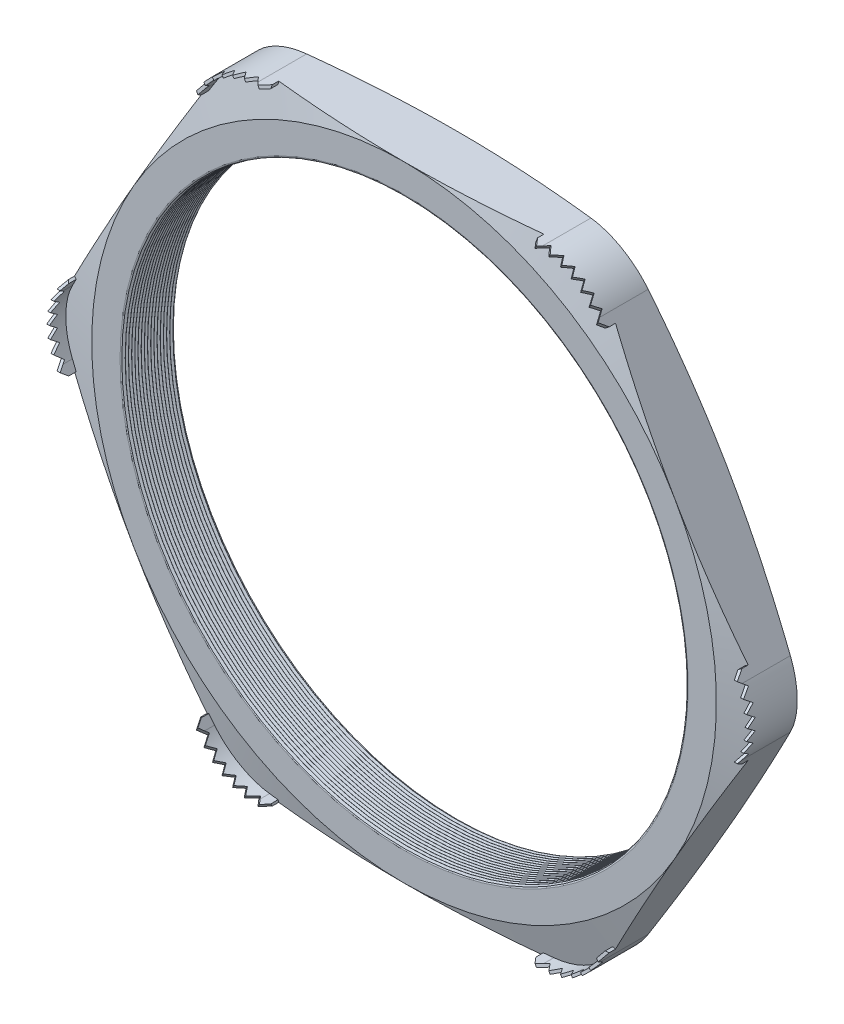
SolidWorks part; units mm, degrees
ref_plane "Front Plane" through (0, 0, 0) normal (0, 0, 1) x (1, 0, 0)
ref_plane "Top Plane" through (0, 0, 0) normal (0, 1, 0) x (1, 0, 0)
ref_plane "Right Plane" through (0, 0, 0) normal (1, 0, 0) x (0, 0, -1)
sketch "Sketch1" plane through (0, 0, 0) normal (0, 0, 1) x (1, 0, 0)
  line L1 (-34.6087, 0) -> (-17.3043, -29.972)
  line L2 (-17.3043, -29.972) -> (17.3043, -29.972)
  line L3 (17.3043, -29.972) -> (34.6087, 0)
  line L4 (34.6087, 0) -> (17.3043, 29.972)
  line L5 (17.3043, 29.972) -> (-17.3043, 29.972)
  line L6 (-17.3043, 29.972) -> (-34.6087, 0)
  circle A0 centre (0, 0) radius 29.972 construction
  circle A1 centre (0, 0) radius 27.051
  dimension "TS" = 54.102
  dimension "H" = 59.944
extrude "Extrude1" add sketch "Sketch1" along normal blind 5.08
fillet "Fillet1" radius 6.35 6 edges at (-17.3043, 29.972, 2.54) (-34.6087, 0, 2.54) (-17.3043, -29.972, 2.54) (17.3043, -29.972, 2.54) (34.6087, 0, 2.54) (17.3043, 29.972, 2.54)
sketch "Sketch2" plane through (0, 0, 5.08) normal (0, 0, 1) x (1, 0, 0)
  line L0 (-13.6382, 29.972) -> (-12.7238, 29.972)
  line L1 (13.6382, 29.972) -> (-13.6382, 29.972) construction
  line L2 (-19.1374, 26.797) -> (-19.5946, 26.0051)
  line L3 (-19.1374, 26.797) -> (-32.7756, 3.175) construction
  line L4 (-13.6382, 29.718) -> (-12.7238, 29.718)
  line L5 (-18.9175, 26.67) -> (-19.3747, 25.8781)
  line L6 (-19.5946, 26.0051) -> (-19.3747, 25.8781)
  line L7 (-12.7238, 29.972) -> (-12.7238, 29.718)
  arc A0 (-13.6382, 29.718) -> (-18.9175, 26.67) centre (-13.6382, 23.622) ccw
  arc A1 (-13.6382, 29.972) -> (-19.1374, 26.797) centre (-13.6382, 23.622) ccw construction
  arc A4 (-13.6382, 29.972) -> (-19.1374, 26.797) centre (-13.6382, 23.622) ccw
  dimension "D1" = 0.9144
  dimension "D2" = 0.9144
  dimension "OFFSET" = 0.254
fillet "Fillet3" radius 0.2032 2 edges at (27.051, 0, 0) (27.051, 0, 5.08)
sketch "Sketch3" plane through (0, 0, 0) normal (0, 1, 0) x (1, 0, 0)
  line L0 (-27.051, -5.08) -> (-27.051, -4.7867)
  line L2 (-27.051, -4.7867) -> (-27.305, -4.9334)
  line L3 (-27.305, -4.9334) -> (-27.051, -5.08)
  line L4 (-27.051, -0.2032) -> (-27.051, -4.8768) construction
  line L5 (-19.1374, -5.08) -> (-32.7756, -5.08) construction
  dimension "D1" = 60
  dimension "D2" = 60
  dimension "D3" = 0.254
revolve "Cut-Revolve1" cut sketch "Sketch3" angle 360 about axis through (0, 0, 5.08) along (0, 0, -1)
pattern_linear "LPattern1" count 17 spacing 0.3048 along (0, 0, -1) of "Cut-Revolve1"
sketch "Sketch4" plane through (0, 0, 0) normal (0, 0, -1) x (-1, 0, 0)
  line L0 (-32.7756, 3.175) -> (-19.1374, 26.797) construction
  circle A0 centre (0, 0) radius 29.972
extrude "Cut-Extrude1" cut sketch "Sketch4" against normal through all draft 75 flip side to cut
sketch "Sketch5" plane through (0, 0, 5.08) normal (0, 0, 1) x (1, 0, 0)
  line L0 (13.6382, 29.972) -> (-13.6382, 29.972) construction
  circle A0 centre (0, 0) radius 29.972
extrude "Cut-Extrude2" cut sketch "Sketch5" against normal through all draft 75 flip side to cut
extrude "Extrude2" add sketch "Sketch2" along normal blind 1.778 and the other way up to next
ref_plane "Plane1" through (-16.0492, 27.7981, 0) normal (0.5, -0.866, 0) x (0.866, 0.5, 0)
sketch "Sketch7" plane through (-16.0492, 27.7981, 0) normal (0.5, -0.866, 0) x (0.866, 0.5, 0)
  line L0 (-3.9669, 4.9911) -> (-3.4081, 5.7379)
  line L1 (-3.9669, 4.3863) -> (-3.9669, 6.858) construction
  line L2 (0, 1.3136) -> (0, 4.0135) construction
  line L4 (-3.4081, 5.7379) -> (-2.8493, 4.9911)
  line L5 (-1.1176, 5.7379) -> (-0.5588, 4.9911)
  line L6 (-2.2352, 5.7379) -> (-1.6764, 4.9911)
  line L7 (-0.5588, 4.9911) -> (0, 5.7379)
  line L8 (0, 5.7379) -> (0.5588, 4.9911)
  line L10 (1.1176, 5.7379) -> (1.6764, 4.9911)
  line L11 (2.2352, 5.7379) -> (2.794, 4.9911)
  line L12 (-2.8493, 4.9911) -> (-2.2352, 5.7379)
  line L13 (-1.6764, 4.9911) -> (-1.1176, 5.7379)
  line L14 (0.5588, 4.9911) -> (1.1176, 5.7379)
  line L15 (3.4081, 5.7379) -> (3.9669, 4.9911)
  line L16 (3.9669, 4.3863) -> (3.9669, 6.858) construction
  line L17 (-3.9669, 4.9911) -> (-3.9669, 6.858)
  line L19 (-3.9669, 6.858) -> (3.9669, 6.858)
  line L20 (3.9669, 6.858) -> (3.9669, 4.9911)
  line L23 (1.6764, 4.9911) -> (2.2352, 5.7379)
  line L25 (2.794, 4.9911) -> (3.4081, 5.7379)
  dimension "D1" = 1.8669
  dimension "D2" = 1.1201
  dimension "D3" = 0.5588
extrude "Cut-Extrude4" cut sketch "Sketch7" against normal through all
pattern_circular "CirPattern1" count 6 over 360 about axis through (0, 0, 0) along (0, 0, 1) of "Extrude2"
pattern_circular "CirPattern2" count 6 over 360 about axis through (0, 0, 0) along (0, 0, 1) of "Cut-Extrude4"
